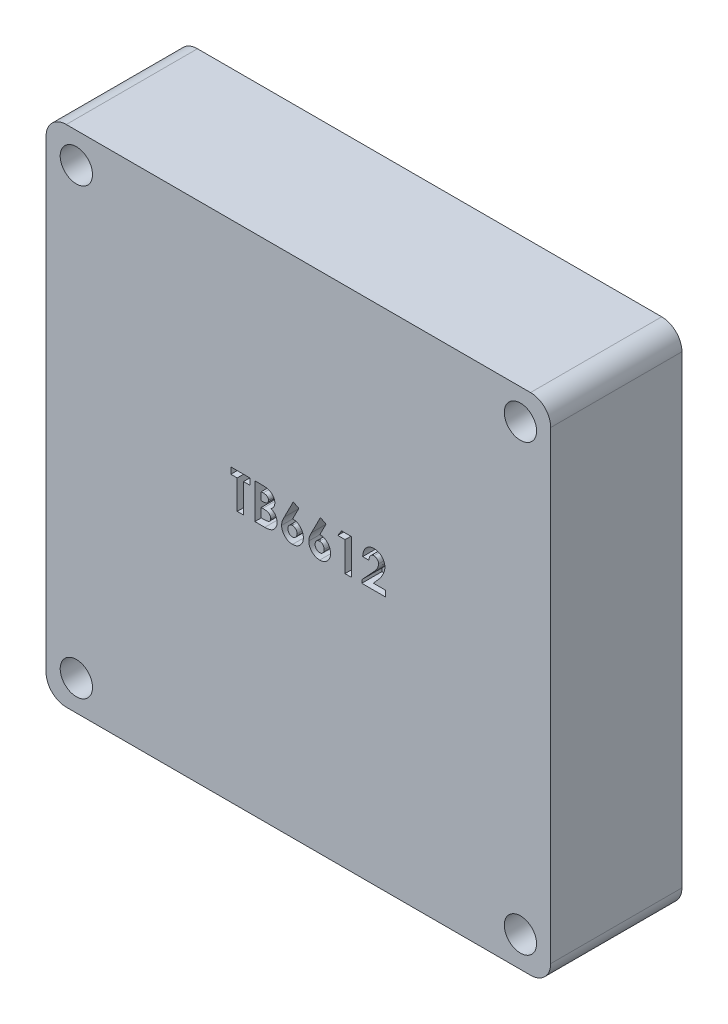
SolidWorks part; units mm, degrees
ref_plane "前视基准面" through (0, 0, 0) normal (0, 0, 1) x (1, 0, 0)
ref_plane "上视基准面" through (0, 0, 0) normal (0, 1, 0) x (1, 0, 0)
ref_plane "右视基准面" through (0, 0, 0) normal (1, 0, 0) x (0, 0, -1)
sketch "草图1" plane through (0, 0, 0) normal (0, 0, 1) x (1, 0, 0)
  line L1 (0, 0) -> (-50, 0)
  line L2 (0, 0) -> (0, 50)
  line L3 (0, 50) -> (-50, 50)
  line L4 (-50, 0) -> (-50, 50)
  line L5 (-47, 47) -> (-3, 47) construction
  line L6 (-47, 47) -> (-47, 3) construction
  line L7 (-47, 3) -> (-3, 3) construction
  line L8 (-3, 47) -> (-3, 3) construction
  circle A0 centre (-47, 47) radius 1.6
  circle A1 centre (-47, 3) radius 1.6
  circle A2 centre (-3, 3) radius 1.6
  circle A3 centre (-3, 47) radius 1.6
  dimension "D7" = 3.2
  dimension "D8" = 3.2
  dimension "D9" = 3.2
  dimension "D10" = 3.2
  dimension "D1" = 50
  dimension "D2" = 50
  dimension "D3" = 44
  dimension "D4" = 44
  dimension "D5" = 3
  dimension "D6" = 3
extrude "凸台-拉伸1" add sketch "草图1" along normal blind 13
fillet "圆角1" radius 2 4 edges at (-50, 50, 6.5) (-50, 0, 6.5) (0, 50, 6.5) (0, 0, 6.5)
sketch "草图2" plane through (0, 0, 13) normal (0, 0, 1) x (1, 0, 0)
  text T0 "<b>TB6612</b>"
extrude "切除-拉伸1" cut sketch "草图2" against normal blind 2
